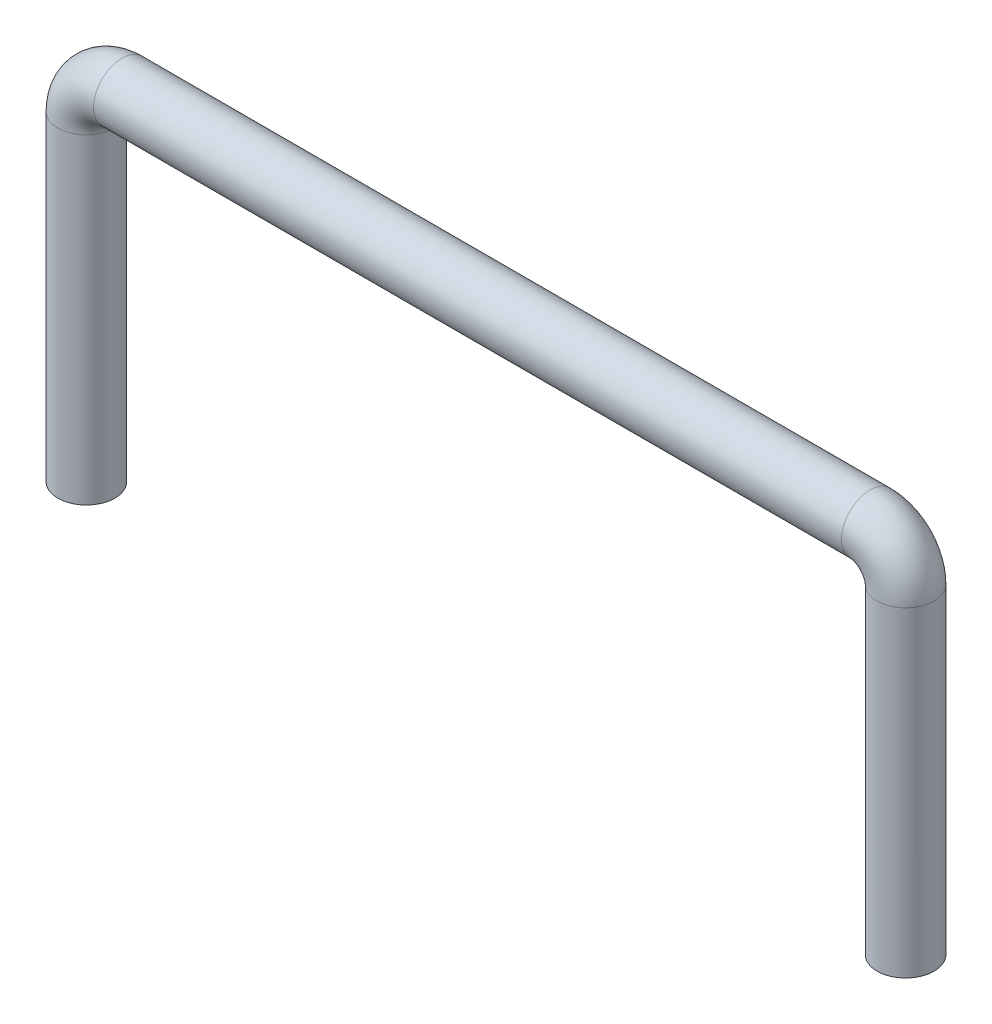
SolidWorks part; units mm, degrees
ref_plane "Front Plane" through (0, 0, 0) normal (0, 0, 1) x (1, 0, 0)
ref_plane "Top Plane" through (0, 0, 0) normal (0, 1, 0) x (1, 0, 0)
ref_plane "Right Plane" through (0, 0, 0) normal (1, 0, 0) x (0, 0, -1)
sketch "Sketch1" plane through (0, 0, 0) normal (0, 1, 0) x (1, 0, 0)
  circle A0 centre (0, 0) radius 0.4
  point P3 (11.5, 0)
  point P4 (5.75, 0)
  point P5 (0, 0)
  point P6 (0, 0)
  point P7 (0, 0)
  dimension "D1" = 0.8
  dimension "D2" = 11.5
  dimension "D3" = 5.75
sketch "Sketch4" plane through (0, 0, 0) normal (0, 0, 1) x (1, 0, 0)
  line L0 (0, 0) -> (0, 4.5)
  line L1 (0.5, 5) -> (11, 5)
  line L2 (11.5, 4.5) -> (11.5, 0)
  arc A0 (0, 4.5) -> (0.5, 5) centre (0.5, 4.5) cw
  arc A1 (11, 5) -> (11.5, 4.5) centre (11, 4.5) cw
  point P7 (0, 5)
  point P10 (11.5, 5)
  dimension "D4" = 0.5
  dimension "D5" = 0.5
  dimension "D1" = 5
  dimension "D2" = 11.5
  dimension "D3" = 5
sweep "Sweep1" add profiles "Sketch1" path "Sketch4"
